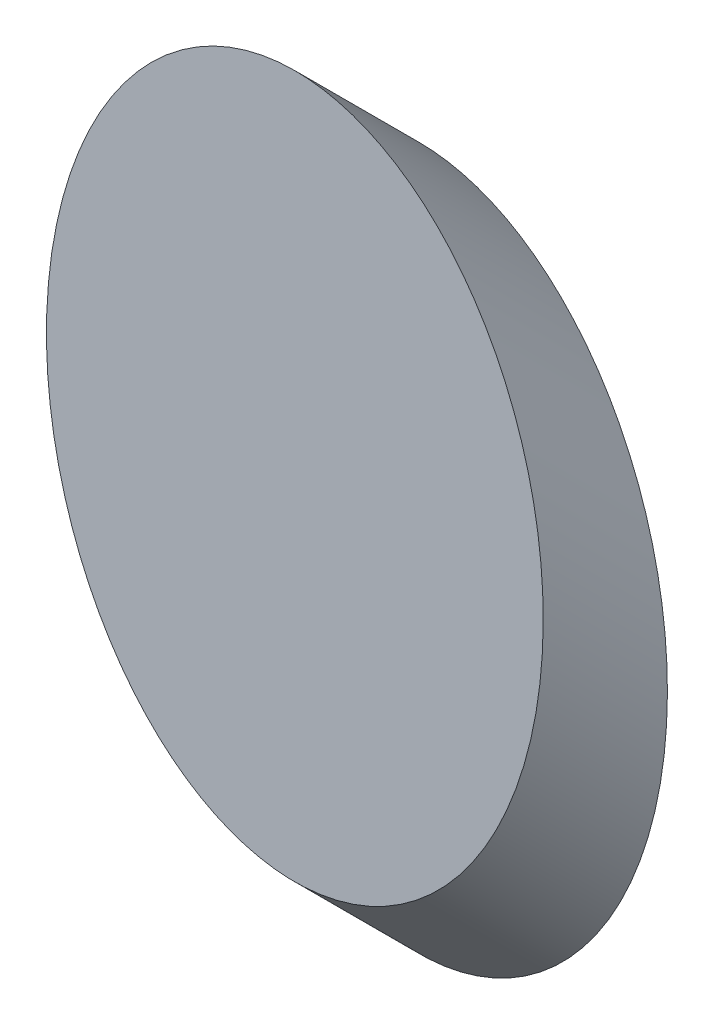
SolidWorks part; units mm, degrees
ref_plane "前视基准面" through (0, 0, 0) normal (0, 0, 1) x (1, 0, 0)
ref_plane "上视基准面" through (0, 0, 0) normal (0, 1, 0) x (1, 0, 0)
ref_plane "右视基准面" through (0, 0, 0) normal (1, 0, 0) x (0, 0, -1)
sketch "草图1" plane through (0, 0, 0) normal (0, 0, 1) x (1, 0, 0)
  ellipse E0 centre (54.3924, 35.7889) end of major axis (54.3924, 92.3639) minor radius 40
  dimension "D1" = 80
  dimension "D2" = 113.15
sketch3d "3D草图2"
  line L0 (55.1123, 92.3547, 0) -> (55.1123, 92.3547, -2.7888) construction
  line L3 (55.1123, 92.3547, 0) -> (55.1123, 72.3547, -20)
  line L4 (55.1123, 92.3547, 0) -> (55.1123, 28.9476, 0) construction
  spline S2 degree 3 poles (54.3924, 92.3639, 0) (-25.6076, 92.3639, 0) (-25.6076, -20.7861, 0) (54.3924, -20.7861, 0) (134.3924, -20.7861, 0) (134.3924, 92.3639, 0) (54.3924, 92.3639, 0) (-25.6076, 92.3639, 0) (-25.6076, -20.7861, 0) knots -0.5 0 0 0 0.5 0.5 0.5 1 1 1 1.5 1.5 1.5 weights 1 0.333333 0.333333 1 0.333333 0.333333 1 0.333333 0.333333 only from (54.3924, 92.3639, 0) to (54.3924, 92.3639, 0) construction
  point P3 (0, 0, 0)
  dimension "D1" = 45
  dimension "D2" = 20
extrude "凸台-拉伸1" add sketch "草图1" along direction (0, -0.7071, -0.7071) on the side against the normal up to vertex (20 mm away) contours E0
